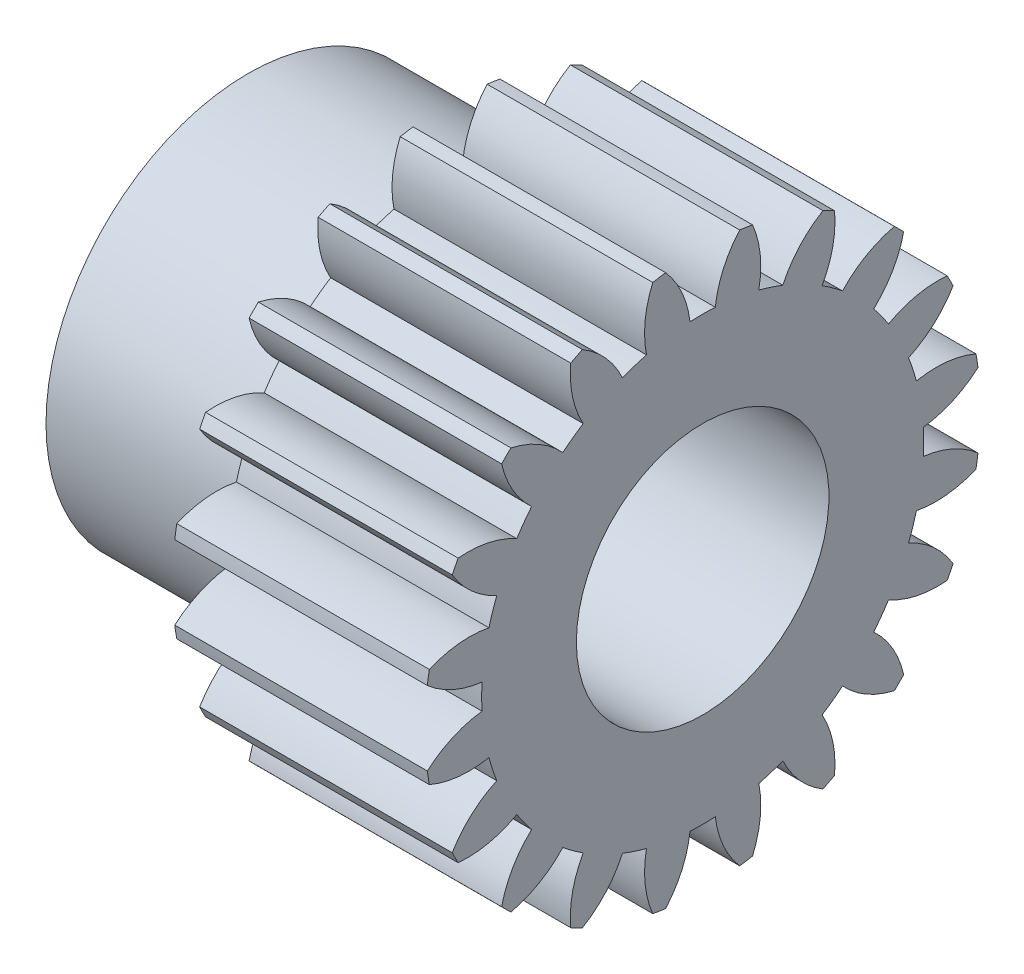
SolidWorks part; units mm, degrees
ref_plane "Plane1" through (0, 0, 0) normal (0, 0, 1) x (1, 0, 0)
ref_plane "Plane2" through (0, 0, 0) normal (0, 1, 0) x (1, 0, 0)
ref_plane "Plane3" through (0, 0, 0) normal (1, 0, 0) x (0, 0, -1)
other "Configuration Table"
sketch "HoldingSke" plane through (0, 0, 0) normal (0, 1, 0) x (1, 0, 0)
  line L0 (0, 0) -> (0.9397, -0.342)
  line L1 (-15, 0) -> (100, 0) construction
  line L2 (0, 0) -> (-2.1039, 2.3779)
  line L3 (0, 0) -> (-11.863, 4.5341)
  line L4 (0, 0) -> (8.1152, 2.9537)
  line L5 (0, 0) -> (-16.8652, -6.2902)
  line L6 (0, 0) -> (-8.2896, -5.593)
  line L7 (-2.1039, 2.3779) -> (1.7706, 19.956)
  line L8 (-76.2, 54.61) -> (-74.4, 54.61)
  line L9 (-71.009, 38.7566) -> (-53.1078, 45.2721)
  line L10 (-76.2, 71.12) -> (104.1128, 71.12)
  line L11 (0, 0) -> (-10, 0)
  line L12 (-76.2, 101.6) -> (-76.162, 101.6)
  line L13 (24.9733, 27.94) -> (52.9518, 28.4284)
  line L14 (24.9733, 27.94) -> (24.9743, 27.94)
  line L15 (24.9733, 27.94) -> (100.4006, 29.5858)
  line L16 (-63.627, -1) -> (-12.827, -1)
  circle A0 centre (0, 0) radius 5
  circle A1 centre (0, 0) radius 8
  circle A2 centre (0, 0) radius 8
  circle A3 centre (0, 0) radius 5
  dimension "MHD" = 16
  dimension "Hub_dia" = 16
  dimension "Bore" = 10
  dimension "MBD" = 10
  dimension "Num_teeth" = 20
  dimension "Pitch" = 1
  dimension "Overall_len" = 18
  dimension "Show_teeth" = 20
  dimension "Thickness" = 10
  dimension "OAL" = 18.0001
  dimension "T_dim" = 1.8
  dimension "Ap" = 20
  dimension "H" = 19.05
  dimension "Pitch_radius" = 180.3128
  dimension "Width" = 10
  dimension "Backlash" = 0.038
  dimension "Addendum_fac" = 1
  dimension "Dedendum_fac" = 1.25
  dimension "Clearance_fac" = 0.25
  dimension "Dedendum_add" = 0.001
  dimension "Module" = 1
sketch "BasProSke" plane through (0, 0, 0) normal (0, 1, 0) x (1, 0, 0)
  line L0 (-10, 0) -> (60, 0) construction
  line L1 (0, 0) -> (0, 11)
  line L2 (0, 0) -> (10, 0)
  line L3 (10, 0) -> (10, 11)
  line L4 (10, 11) -> (0, 11)
  dimension "Thickness" = 10
  dimension "Diameter" = 22
revolve "Base-Revolve" add sketch "BasProSke" angle 360 about L0
sketch "TooCutSke" plane through (0, 0, 0) normal (1, 0, 0) x (0, 0, -1)
  line L1 (0, 0) -> (0, 107) construction
  line L2 (0, 0) -> (-0.8511, 9.9637) construction
  line L3 (0, 0) -> (-3.1206, 19.7028) construction
  line L4 (-0.8511, 9.9637) -> (-1.5603, 9.8514) construction
  arc A0 (0.4999, 8.7347) -> (-0.4999, 8.7347) centre (0, 0) ccw
  arc A1 (1.4852, 10.9249) -> (-1.4852, 10.9249) centre (0, 0) ccw
  circle A2 centre (0, 0) radius 10 construction
  circle A3 centre (0, 0) radius 9.3969 construction
  arc A4 (-0.4999, 8.7347) -> (-1.4852, 10.9249) centre (-4.4722, 8.2645) ccw
  arc A5 (1.4852, 10.9249) -> (0.4999, 8.7347) centre (4.4722, 8.2645) ccw
  dimension "Root_dia" = 17.498
  dimension "Overcut_dia" = 22.0508
  dimension "Pitch_dia" = 20
  dimension "Base_dia" = 18.7939
  dimension "Flank_rad" = 4
  dimension "Half_ang" = 9
  dimension "Half_CT" = 0.7181
extrude "ToothCut" cut sketch "TooCutSke" along normal through all
fillet "Breaks" [suppressed] radius 0.02
fillet "RootFillets" [suppressed] radius 0.251
pattern_circular "TeethCuts" count 20 every 18 about axis through (-10, 0, 0) along (1, 0, 0) of "ToothCut", "RootFillets", "Breaks"
sketch "HubNeaOneSke" plane through (0, 0, 0) normal (-1, 0, 0) x (0, 0, 1)
  circle A0 centre (0, 0) radius 8
  dimension "Diameter" = 16
extrude "HubNearOne" add sketch "HubNeaOneSke" along normal blind 8.0001
sketch "HubNeaBotSke" plane through (0, 0, 0) normal (-1, 0, 0) x (0, 0, 1)
  circle A0 centre (0, 0) radius 8
  dimension "Diameter" = 16
extrude "HubNearBoth" [suppressed] add sketch "HubNeaBotSke" along normal blind 4
ref_plane "FarPln" through (10, 0, 0) normal (1, 0, 0) x (0, 0, -1)
sketch "HubFarSke" plane through (10, 0, 0) normal (1, 0, 0) x (0, 0, -1)
  circle A0 centre (0, 0) radius 8
  dimension "Diameter" = 16
extrude "HubFar" [suppressed] add sketch "HubFarSke" along normal blind 4
sketch "BorSke" plane through (0, 0, 0) normal (1, 0, 0) x (0, 0, -1)
  circle A0 centre (0, 0) radius 5
  dimension "Diameter" = 10
extrude "Bore" cut sketch "BorSke" along normal mid plane 36.0001
sketch "KeySke" plane through (0, 0, 0) normal (1, 0, 0) x (0, 0, -1)
  line L0 (-2, 0) -> (-2, 6.8)
  line L1 (-2, 6.8) -> (2, 6.8)
  line L2 (2, 6.8) -> (2, 0)
  line L3 (0, 0) -> (0, 34) construction
  line L4 (-2, 0) -> (2, 0)
  dimension "Offset" = 6.8
  dimension "Width" = 4
extrude "Keyway" [suppressed] cut sketch "KeySke" along normal mid plane 36.0001
pattern_circular "Keyway2" [suppressed] count 2 every 90 about axis through (-10, 0, 0) along (1, 0, 0)
equation "' \"Module@HoldingSke\" = 6.35"
equation "' \"Num_teeth@HoldingSke\" = 12"
equation "' \"Ap@HoldingSke\" =  20"
equation "' \"Ap@HoldingSke\" = 20"
equation "' \"Width@HoldingSke\" = 0.5 * 25.4"
equation "' \"Hub_dia@HoldingSke\"= 1 * 25.4"
equation "' \"Hub_dia@HoldingSke\" = 1 * 25.4"
equation "' \"Overall_len@HoldingSke\" = 1.0 * 25.4"
equation "' \"Bore@HoldingSke\" = 0.75 * 25.4"
equation "' \"T_dim@HoldingSke\" = 0.1 * 25.4"
equation "' \"Width@KeySke\" = 0.25 * 25.4"
equation "' \"Show_teeth@HoldingSke\" = 13"
equation "' \"Backlash@HoldingSke\" = 0.009 * 25.4"
equation "' \"Addendum_fac@HoldingSke\" = 1.0"
equation "' \"Dedendum_fac@HoldingSke\" = 1.25"
equation "' \"Dedendum_add@HoldingSke\" = 0.00005 * 25.4"
equation "' \"Clearance_fac@HoldingSke\" = 0.25"
equation "\"Pitch@HoldingSke\" = 1 / \"Module@HoldingSke\""
equation "\"Overcut_dia@TooCutSke\" = (\"Num_teeth@HoldingSke\" + 2 * \"Addendum_fac@HoldingSke\") / \"Pitch@HoldingSke\" + 0.002 * 25.4"
equation "\"Pitch_dia@TooCutSke\" = \"Num_teeth@HoldingSke\" / \"Pitch@HoldingSke\""
equation "\"Base_dia@TooCutSke\" = \"Num_teeth@HoldingSke\" / \"Pitch@HoldingSke\" * cos((\"Ap@HoldingSke\"  * 3.14159265 / 180))"
equation "\"Root_dia@TooCutSke\" = (\"Num_teeth@HoldingSke\" + 2) / \"Pitch@HoldingSke\" - 2 * (\"Addendum_fac@HoldingSke\" + \"Dedendum_fac@HoldingSke\") / \"Pitch@HoldingSke\" - \"Dedendum_add@HoldingSke\" * 2"
equation "\"Half_ang@TooCutSke\" = 180 / \"Num_teeth@HoldingSke\""
equation "\"Half_CT@TooCutSke\" = \"Num_teeth@HoldingSke\" / \"Pitch@HoldingSke\" * sin((3.14159265 / 2 / \"Num_teeth@HoldingSke\")) / 2 - 7 * \"Backlash@HoldingSke\" / 4"
equation "\"Flank_rad@TooCutSke\" = \"Num_teeth@HoldingSke\" / \"Pitch@HoldingSke\" / 5"
equation "\"Radius@RootFillets\" = \"Clearance_fac@HoldingSke\" / \"Pitch@HoldingSke\" + \"Dedendum_add@HoldingSke\""
equation "\"Break_rad@Breaks\" = 0.02 / \"Pitch@HoldingSke\""
equation "\"Thickness@HoldingSke\" = \"Width@HoldingSke\""
equation "\"OAL@HoldingSke\" = \"Thickness@HoldingSke\""
equation "\"MHD@HoldingSke\" = (\"Num_teeth@HoldingSke\" + 2) / \"Pitch@HoldingSke\" - 2 * (\"Addendum_fac@HoldingSke\" + \"Dedendum_fac@HoldingSke\")  / \"Pitch@HoldingSke\" - \"Dedendum_add@HoldingSke\" * 2"
equation "\"MBD@HoldingSke\" = (\"Num_teeth@HoldingSke\" + 2) / \"Pitch@HoldingSke\" - 2 * (\"Addendum_fac@HoldingSke\" + \"Dedendum_fac@HoldingSke\")  / \"Pitch@HoldingSke\" - \"Dedendum_add@HoldingSke\" * 2 - 0.002 * 25.4"
equation "\"MHD@HoldingSke\" = ((sgn( \"MHD@HoldingSke\" - \"Hub_dia@HoldingSke\" )-1)*( \"MHD@HoldingSke\" - \"Hub_dia@HoldingSke\" ))/-2+ \"Hub_dia@HoldingSke\""
equation "\"MBD@HoldingSke\" = ((sgn( \"MBD@HoldingSke\" - \"Bore@HoldingSke\" )-1)*( \"MBD@HoldingSke\" - \"Bore@HoldingSke\" ))/-2+ \"Bore@HoldingSke\""
equation "\"OAL@HoldingSke\" = ((sgn( \"OAL@HoldingSke\" - \"Overall_len@HoldingSke\" )+1)*( \"OAL@HoldingSke\" - \"Overall_len@HoldingSke\" ))/2 + \"Overall_len@HoldingSke\" + 0.000002 * 25.4"
equation "\"Num_teeth@TeethCuts\" = int( \"Show_teeth@HoldingSke\" ) + 1"
equation "\"Num_teeth@TeethCuts\" = ((sgn( \"Num_teeth@TeethCuts\" - \"Num_teeth@HoldingSke\" )-1)*( \"Num_teeth@TeethCuts\" - \"Num_teeth@HoldingSke\" ))/-2+ \"Num_teeth@HoldingSke\""
equation "\"Num_teeth@TeethCuts\" = ((sgn( \"Num_teeth@TeethCuts\" - 2.0)+1)*( \"Num_teeth@TeethCuts\" - 2.0))/2 +2.0"
equation "\"Angle@TeethCuts\" = 360.0 / \"Num_teeth@HoldingSke\""
equation "\"Diameter@BasProSke\" = (\"Num_teeth@HoldingSke\" + 2 * \"Addendum_fac@HoldingSke\") / \"Pitch@HoldingSke\""
equation "\"Thickness@BasProSke\"  = \"Thickness@HoldingSke\""
equation "' \"Fillet_rad@BasProSke\" =  \"Thickness@HoldingSke\" * 0.05"
equation "' \"Fillet_rad@BasProSke\" = \"Thickness@HoldingSke\" * 0.05"
equation "\"MHD@HoldingSke\" = ((sgn( \"MHD@HoldingSke\" - \"Root_dia@TooCutSke\" )-1)*( \"MHD@HoldingSke\" - \"Root_dia@TooCutSke\" ))/-2+ \"Root_dia@TooCutSke\""
equation "\"Diameter@HubNeaOneSke\" = \"MHD@HoldingSke\""
equation "\"Length@HubNearOne\" = \"OAL@HoldingSke\" - \"Thickness@BasProSke\""
equation "\"Diameter@HubNeaBotSke\" = \"MHD@HoldingSke\""
equation "\"Length@HubNearBoth\" = ( \"OAL@HoldingSke\" - \"Thickness@BasProSke\" ) / 2.0"
equation "\"Thickness@FarPln\" = \"Thickness@BasProSke\""
equation "\"Diameter@HubFarSke\" = \"MHD@HoldingSke\""
equation "\"Length@HubFar\" = ( \"OAL@HoldingSke\" - \"Thickness@BasProSke\" ) / 2.0"
equation "\"Diameter@BorSke\" = \"MBD@HoldingSke\""
equation "\"D1@Bore\" = \"OAL@HoldingSke\" * 2.0"
equation "\"D1@Keyway\" = \"OAL@HoldingSke\" * 2.0"
equation "\"Offset@KeySke\" = \"T_dim@HoldingSke\" + \"MBD@HoldingSke\" / 2.0"
